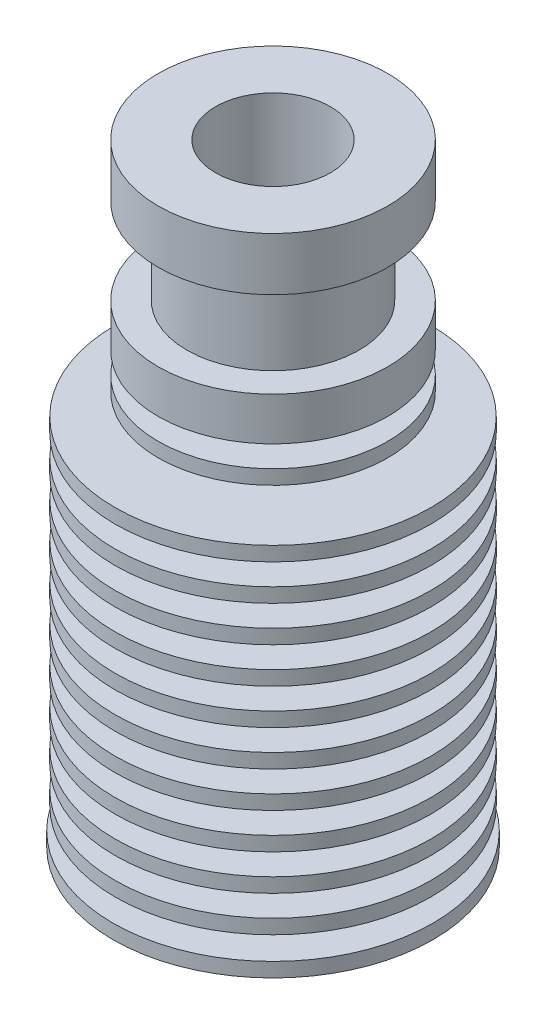
SolidWorks part; units mm, degrees
material "6061 Alloy"
ref_plane "Front Plane" through (0, 0, 0) normal (0, 0, 1) x (1, 0, 0)
ref_plane "Top Plane" through (0, 0, 0) normal (0, 1, 0) x (1, 0, 0)
ref_plane "Right Plane" through (0, 0, 0) normal (1, 0, 0) x (0, 0, -1)
sketch "Sketch1" plane through (0, 0, 0) normal (0, 0, 1) x (1, 0, 0)
  line L0 (0, 0) -> (0, -50000) construction
  line L1 (0, 0) -> (11.15, 0)
  line L2 (11.15, 0) -> (11.15, 1)
  line L3 (8, 30) -> (3.5, 30)
  line L4 (8, 30) -> (8, 33)
  line L5 (8, 33) -> (6, 33)
  line L6 (6, 33) -> (6, 39)
  line L7 (6, 39) -> (8, 39)
  line L8 (8, 39) -> (8, 42.7)
  line L9 (8, 42.7) -> (0, 42.7)
  line L10 (0, 42.7) -> (0, 0)
  line L12 (11, 1) -> (11, 26)
  line L13 (3.5, 26) -> (11, 26)
  line L14 (3.5, 27.5) -> (8, 27.5)
  line L15 (8, 27.5) -> (8, 28.5)
  line L16 (8, 28.5) -> (3.5, 28.5)
  line L17 (3.5, 28.5) -> (3.5, 30)
  line L18 (3.5, 27.5) -> (3.5, 26)
  line L20 (11.15, 1) -> (11, 1)
  dimension "D1" = 22.3
  dimension "D2" = 16
  dimension "D3" = 12
  dimension "D4" = 16
  dimension "D5" = 3.7
  dimension "D6" = 6
  dimension "D7" = 3
  dimension "D8" = 42.7
  dimension "D9" = 26
  dimension "D10" = 1.5
  dimension "D11" = 1
  dimension "D12" = 7
  dimension "D13" = 22
  dimension "D14" = 1
revolve "Revolve1" add sketch "Sketch1" angle 360 about L0
sketch "Sketch2" plane through (0, 0, 0) normal (0, 0, 1) x (1, 0, 0)
  line L0 (11, 1) -> (11, 26) construction
  line L3 (11, 1) -> (6, 1)
  line L4 (6, 1) -> (6, 2.5)
  line L5 (6, 2.5) -> (11, 2.5)
  line L6 (0, 0) -> (0, 26) construction
  line L7 (11.15, 26) -> (-11.15, 26) construction
  line L8 (11, 2.5) -> (11, 1)
  dimension "D1" = 2.5
  dimension "D3" = 12
revolve "Cut-Revolve1" cut sketch "Sketch2" angle 360 about L6
pattern_linear "LPattern1" count 10 spacing 2.5 along (0, 1, 0) of "Cut-Revolve1"
sketch "Sketch3" plane through (0, 0, 0) normal (0, 0, 1) x (1, 0, 0)
  line L0 (0, 42.7) -> (0, 0)
  line L1 (8, 42.7) -> (-8, 42.7) construction
  line L2 (0, 0) -> (2.1, 0)
  line L3 (-11.15, 0) -> (11.15, 0) construction
  line L4 (2.1, 0) -> (2.1, 34.3)
  line L6 (4, 36.2) -> (4, 42.7)
  line L7 (4, 42.7) -> (0, 42.7)
  line L8 (4, 36.2) -> (2.1, 34.3)
  dimension "D1" = 4
  dimension "D2" = 2.1
  dimension "D3" = 6.5
  dimension "D4" = 45
revolve "Cut-Revolve2" cut sketch "Sketch3" angle 360 about L0
hole_wizard "M7x1.0 Tapped Hole1" positions "Sketch5" profile "Sketch4" tap size "M7x1.0" standard "ANSI Metric"
sketch "Sketch5" plane through (0, 0, 0) normal (0, -1, 0) x (-1, 0, 0)
  point P0 (0, 0)
sketch "Sketch4" plane through (0, 0, 0) normal (1, 0, 0) x (0, 0, -1)
  line L0 (0, 0) -> (0, 16.9026)
  line L1 (0, 16.9026) -> (3, 15.1)
  line L2 (3, 15.1) -> (3, 0)
  line L5 (3, 0) -> (0, 0)
  line L10 (0, 16.9026) -> (-3, 15.1) construction
  line L11 (0, -6.35) -> (0, 107.95) construction
  dimension "Tap Drill Dia." = 6
  dimension "Tap Drill Depth" = 15.1
  dimension "Drill Angle" = 118
cosmetic thread "Hole Thread1" parameters "D1"=14, "D2"=7
